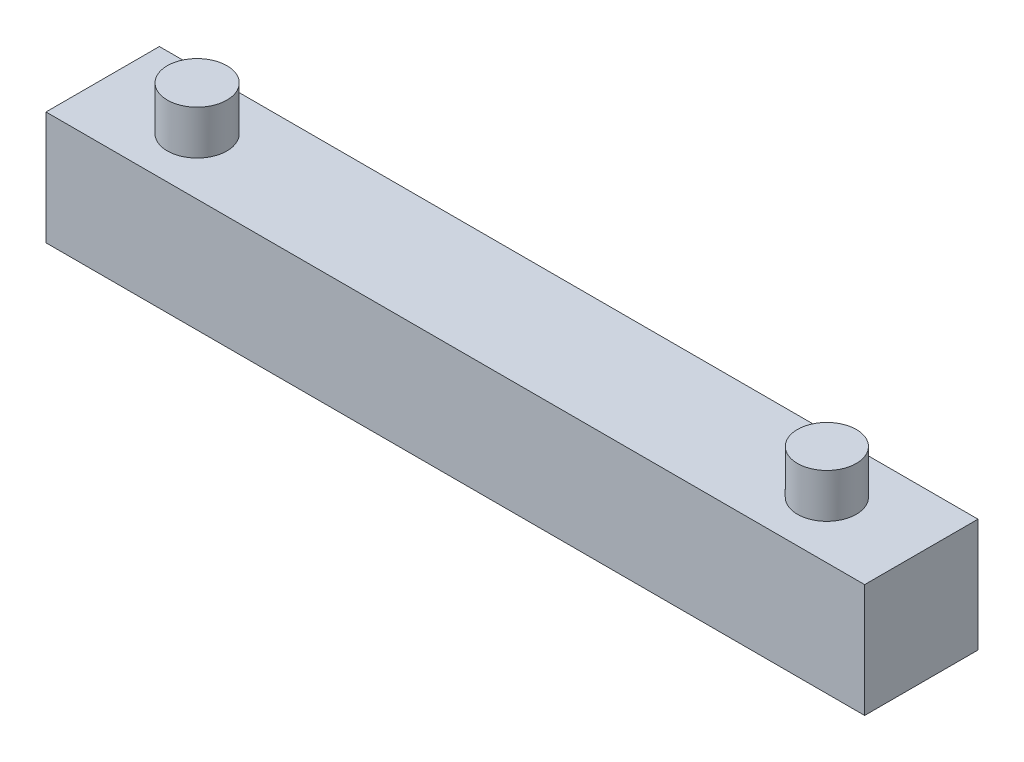
SolidWorks part; units mm, degrees
ref_plane "Front Plane" through (0, 0, 0) normal (0, 0, 1) x (1, 0, 0)
ref_plane "Top Plane" through (0, 0, 0) normal (0, 1, 0) x (1, 0, 0)
ref_plane "Right Plane" through (0, 0, 0) normal (1, 0, 0) x (0, 0, -1)
sketch "Sketch2" plane through (0, 0, 0) normal (0, 1, 0) x (1, 0, 0)
  line L1 (0, 0) -> (65, 0)
  line L2 (0, 0) -> (0, 9)
  line L3 (0, 9) -> (65, 9)
  line L4 (65, 0) -> (65, 9)
  dimension "D1" = 65
  dimension "D2" = 9
extrude "Boss-Extrude1" add sketch "Sketch2" along normal blind 9
sketch "Sketch3" plane through (0, 9, 0) normal (0, 1, 0) x (1, 0, 0)
  line L0 (0, 4.5) -> (7.5, 4.5)
  line L2 (0, 9) -> (0, 0) construction
  line L3 (7.5, 4.5) -> (7.5, 0)
  line L4 (0, 0) -> (65, 0) construction
  circle A0 centre (7.5, 4.5) radius 2.3665
  circle A1 centre (57.5, 4.5) radius 2.3373
  dimension "D1" = 7.5
  dimension "D2" = 50
extrude "Boss-Extrude2" add sketch "Sketch3" along normal blind 3.5 contours A0 | A1
